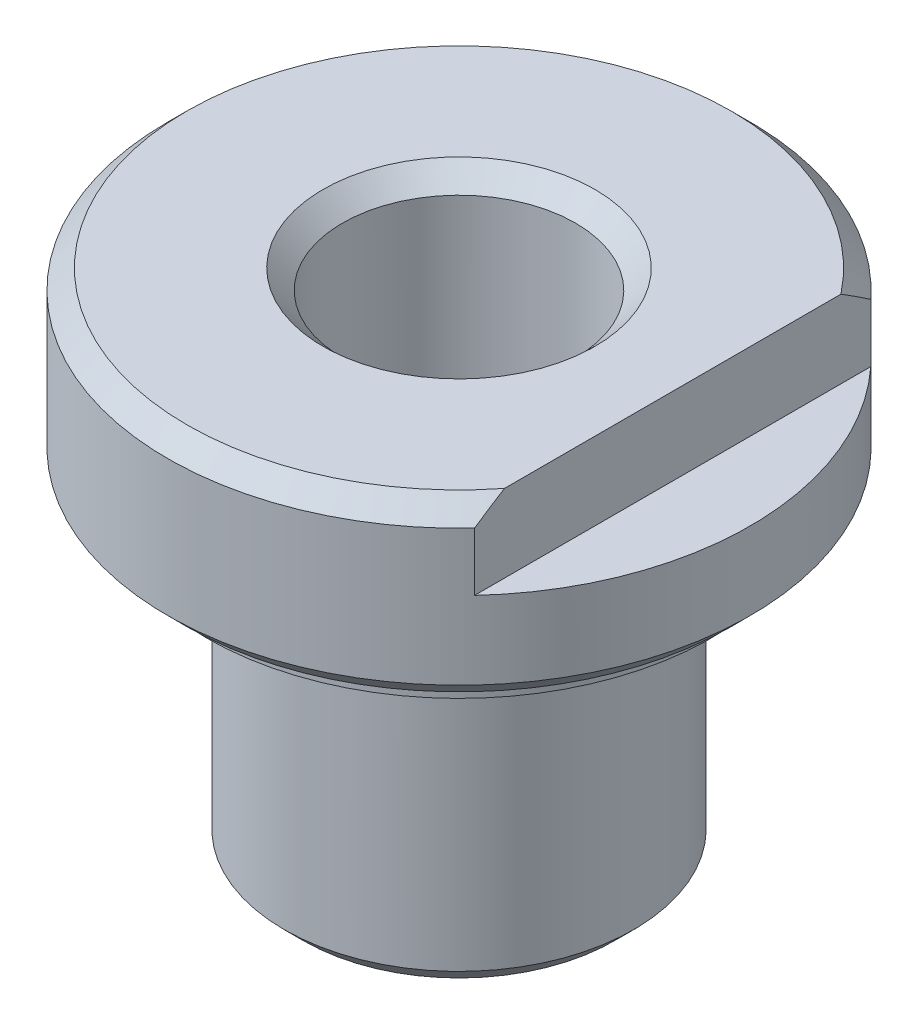
SolidWorks part; units mm, degrees
ref_plane "前视基准面" through (0, 0, 0) normal (0, 0, 1) x (1, 0, 0)
ref_plane "上视基准面" through (0, 0, 0) normal (0, 1, 0) x (1, 0, 0)
ref_plane "右视基准面" through (0, 0, 0) normal (1, 0, 0) x (0, 0, -1)
sketch "草图1" plane through (0, 0, 0) normal (0, 0, 1) x (1, 0, 0)
  line L0 (0, 0) -> (9, 0)
  line L1 (9, 0) -> (9, 15)
  line L2 (9, 15) -> (8, 15)
  line L3 (8, 15) -> (8, 16)
  line L4 (10, 16) -> (13, 16)
  line L5 (15, 17) -> (15, 26)
  line L6 (15, 26) -> (0, 26)
  line L7 (0, 26) -> (0, 0)
  line L8 (15, 17) -> (13, 17)
  line L9 (13, 17) -> (13, 16)
  line L10 (8, 16) -> (8, 16.5)
  line L11 (8, 16.5) -> (10, 16.5)
  line L12 (10, 16.5) -> (10, 16)
  dimension "D1" = 9
  dimension "D2" = 16
  dimension "D3" = 15
  dimension "D4" = 13
  dimension "D5" = 10
  dimension "D6" = 0.5
  dimension "D7" = 1
  dimension "D8" = 1
  dimension "D9" = 1
  dimension "D10" = 2
revolve "旋转1" add sketch "草图1" angle 360 about L7
sketch "草图2" plane through (0, 0, 0) normal (0, -1, 0) x (1, 0, 0)
  circle A0 centre (0, 0) radius 6
  dimension "D1" = 12
extrude "切除-拉伸1" cut sketch "草图2" against normal through all
sketch "草图3" plane through (0, 26, 0) normal (0, 1, 0) x (1, 0, 0)
  line L0 (11, 10.198) -> (11, -10.198)
  circle A0 centre (0, 0) radius 15 construction
  arc A1 (11, -10.198) -> (11, 10.198) centre (0, 0) ccw
  dimension "D1" = 11
extrude "切除-拉伸2" cut sketch "草图3" against normal blind 4
chamfer "倒角3" distance 1 angle 45 4 edges at (0, 0, 9) (0, 17, 15) (-15, 26, 0) (0, 26, -6)
chamfer "倒角4" distance 0.5 angle 45 2 edges at (0, 0, -6) (0, 15, 9)
